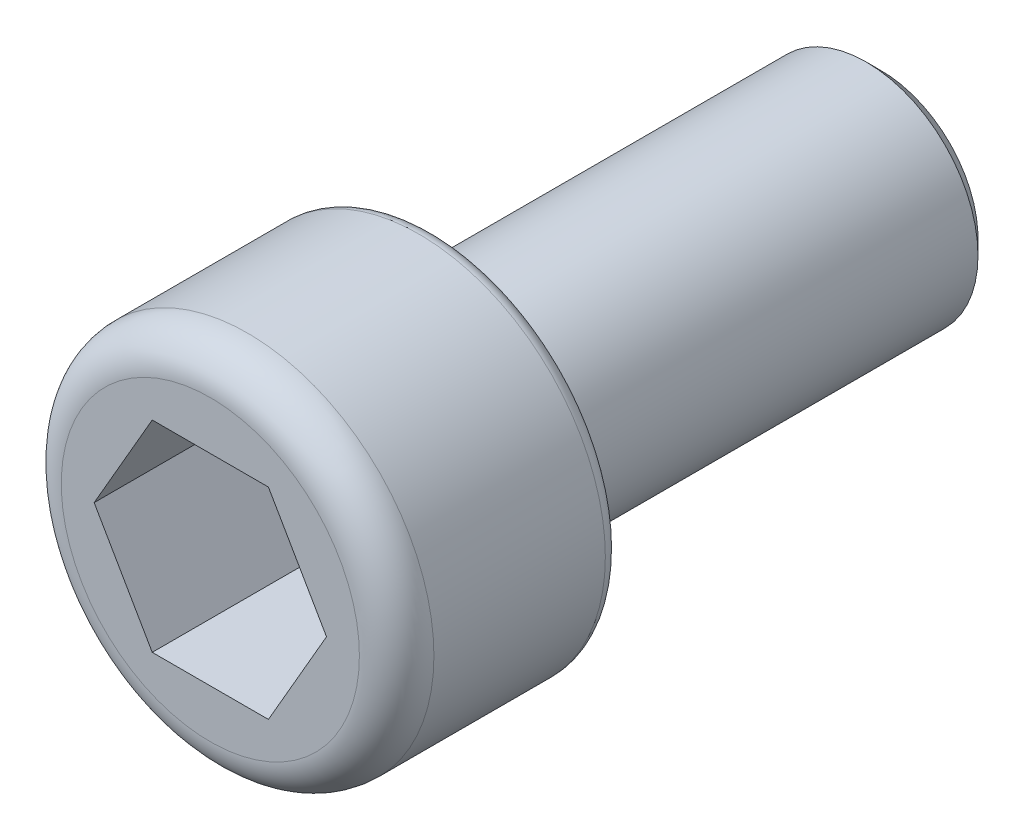
SolidWorks part; units mm, degrees
ref_plane "前视" through (0, 0, 0) normal (0, 0, 1) x (1, 0, 0)
ref_plane "上视" through (0, 0, 0) normal (0, 1, 0) x (1, 0, 0)
ref_plane "右视" through (0, 0, 0) normal (1, 0, 0) x (0, 0, -1)
sketch "草图1" plane through (0, 0, 0) normal (0, 0, 1) x (1, 0, 0)
  circle A0 centre (0, 0) radius 2.5
  dimension "D1" = 5
extrude "凸台-拉伸1" add sketch "草图1" along normal blind 3
fillet "圆角1" radius 0.5 1 edges at (2.5, 0, 3)
sketch "草图2" plane through (0, 0, 3) normal (0, 0, 1) x (1, 0, 0)
  line L1 (1.5588, 0) -> (0.7794, 1.35)
  line L2 (0.7794, 1.35) -> (-0.7794, 1.35)
  line L3 (-0.7794, 1.35) -> (-1.5588, 0)
  line L4 (-1.5588, 0) -> (-0.7794, -1.35)
  line L5 (-0.7794, -1.35) -> (0.7794, -1.35)
  line L6 (0.7794, -1.35) -> (1.5588, 0)
  circle A0 centre (0, 0) radius 1.35 construction
  dimension "D1" = 2.7
extrude "切除-拉伸1" cut sketch "草图2" against normal blind 2
sketch "草图3" plane through (0, 0, 0) normal (0, 0, -1) x (-1, 0, 0)
  circle A0 centre (0, 0) radius 1.5
  dimension "D1" = 3
extrude "凸台-拉伸2" add sketch "草图3" along normal blind 6
chamfer "倒角1" distance 0.2 angle 45 1 edges at (-1.5, 0, -6)
fillet "圆角2" radius 0.2 1 edges at (2.5, 0, 0)
